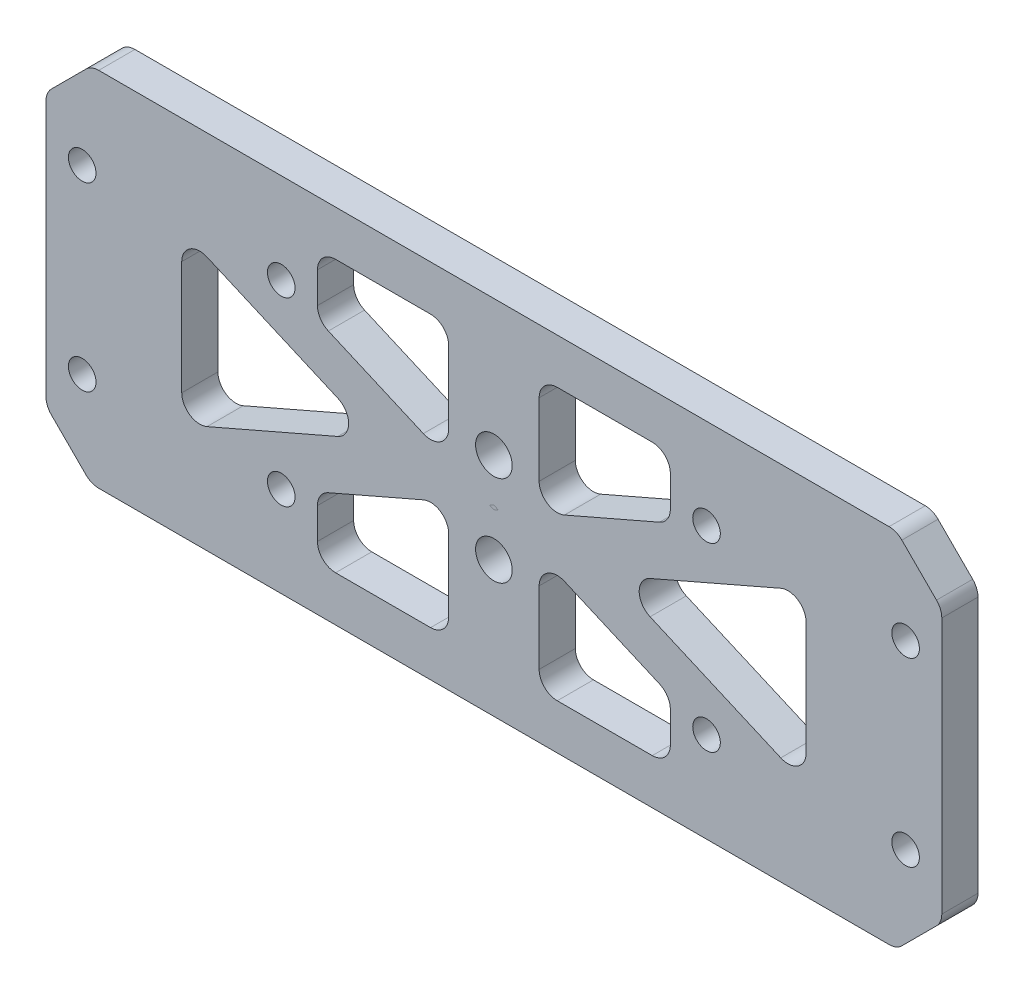
SolidWorks part; units mm, degrees
material "Thornel Mat VMA"
ref_plane "前视基准面" through (0, 0, 0) normal (0, 0, 1) x (1, 0, 0)
ref_plane "上视基准面" through (0, 0, 0) normal (0, 1, 0) x (1, 0, 0)
ref_plane "右视基准面" through (0, 0, 0) normal (1, 0, 0) x (0, 0, -1)
other "Configuration Table"
sketch "草图1" plane through (0, 0, 0) normal (0, 0, 1) x (1, 0, 0)
  line L17 (-49.5, -20) -> (49.5, -20)
  line L18 (-49.5, -20) -> (-49.5, 20)
  line L19 (-49.5, 20) -> (49.5, 20)
  line L20 (49.5, -20) -> (49.5, 20)
  line L21 (-49.5, -20) -> (49.5, 20) construction
  line L22 (-49.5, 20) -> (49.5, -20) construction
  point P0 (0, 0)
  dimension "D1" = 99
  dimension "D2" = 40
extrude "凸台-拉伸1" add sketch "草图1" along normal blind 4
chamfer "倒角1" distance 5 angle 45 4 edges at (49.5, -20, 2) (49.5, 20, 2) (-49.5, -20, 2) (-49.5, 20, 2)
sketch "草图3" plane through (0, 0, 4) normal (0, 0, 1) x (1, 0, 0)
  line L0 (0, 0) -> (-49.5, 0) construction
  line L1 (-49.5, 15) -> (-49.5, -15) construction
  line L2 (0, 0) -> (0, 20) construction
  line L3 (44.5, 20) -> (-44.5, 20) construction
  circle A0 centre (-45.5, 10) radius 1.525
  circle A1 centre (-45.5, -10) radius 1.525
  circle A2 centre (45.5, -10) radius 1.525
  circle A3 centre (45.5, 10) radius 1.525
  dimension "D1" = 3.05
  dimension "D2" = 20
  dimension "D3" = 4
extrude "切除-拉伸1" cut sketch "草图3" against normal blind 10
sketch "草图4" plane through (0, 0, 4) normal (0, 0, 1) x (1, 0, 0)
  line L0 (44.5, 20) -> (-44.5, 20) construction
  line L1 (-34.5, -15) -> (34.5, -15) construction
  line L2 (-34.5, -15) -> (-34.5, 15) construction
  line L3 (-34.5, 15) -> (34.5, 15) construction
  line L4 (34.5, -15) -> (34.5, 15) construction
  line L5 (-34.5, -15) -> (34.5, 15) construction
  line L6 (-34.5, 15) -> (34.5, -15) construction
  line L7 (49.5, -15) -> (49.5, 15) construction
  line L8 (-35, 15) -> (35, 15)
  line L9 (35, 15) -> (0, -0.2174)
  line L10 (0, -0.2174) -> (-35, 15)
  line L11 (-34.5, 9.3305) -> (-34.5, -9.3305)
  line L12 (-34.5, -9.3305) -> (-13.0399, 0)
  line L13 (-13.0399, 0) -> (-34.5, 9.3305)
  line L14 (0, 0) -> (0, -15) construction
  line L15 (0, 0) -> (-13.0399, 0) construction
  line L16 (-35, -15) -> (35, -15)
  line L17 (35, -15) -> (0, 0.2174)
  line L18 (0, 0.2174) -> (-35, -15)
  line L19 (34.5, 9.3305) -> (34.5, -9.3305)
  line L20 (13.0399, 0) -> (34.5, 9.3305)
  line L21 (34.5, -9.3305) -> (13.0399, 0)
  point P0 (0, 0)
  dimension "D1" = 5
  dimension "D2" = 15
  dimension "D3" = 5
  dimension "D4" = 70
extrude "切除-拉伸2" cut sketch "草图4" against normal blind 10 contours L18 L17 L9 L8 L10 | L10 L18 L16 L17 L9 | L12 L13 L11 | L21 L19 L20
sketch "草图5" plane through (0, 0, 4) normal (0, 0, 1) x (1, 0, 0)
  line L0 (35, 15) -> (-35, 15) construction
  line L3 (-5, -15) -> (5, -15)
  line L4 (-5, -15) -> (-5, 15)
  line L6 (-5, 15) -> (5, 15)
  line L7 (5, -15) -> (5, 15)
  line L8 (-5, -15) -> (5, 15) construction
  line L9 (-5, 15) -> (5, -15) construction
  point P0 (0, 0)
  dimension "D1" = 10
extrude "凸台-拉伸2" add sketch "草图5" against normal up to surface (4 mm away) up to face at (0, 0, 0)
fillet "圆角2" radius 2 18 edges at (34.5, -9.3305, 2) (34.5, 9.3305, 2) (13.0399, 0, 2) (-34.5, -9.3305, 2) (-13.0399, 0, 2) (-34.5, 9.3305, 2) (5, 1.9565, 2) (35, 15, 2) (5, 15, 2) (-35, -15, 2) (-5, -15, 2) (-5, -1.9565, 2) (5, -15, 2) (35, -15, 2) (5, -1.9565, 2) (-5, 15, 2) (-35, 15, 2) (-5, 1.9565, 2)
fillet "圆角3" radius 2 8 edges at (49.5, 15, 2) (44.5, 20, 2) (-49.5, 15, 2) (-49.5, -15, 2) (-44.5, -20, 2) (44.5, -20, 2) (49.5, -15, 2) (-44.5, 20, 2)
sketch "草图6" plane through (0, 0, 0) normal (0, 0, -1) x (-1, 0, 0)
  line L0 (-19.5, 8.2609) -> (-19.5, 15)
  line L1 (-7.7975, 3.1728) -> (-26.1815, 11.1659) construction
  line L2 (-19.5, -312.5) -> (-19.5, 87.5) construction
  line L3 (-25.384, 15) -> (-7, 15) construction
  line L4 (-19.5, 15) -> (-35, 15)
  line L5 (-35, 15) -> (-19.5, 8.2609)
  line L6 (0, 0) -> (-16.0559, 0) construction
  line L7 (0, 0) -> (0, 20) construction
  line L8 (-43.6716, 20) -> (43.6716, 20) construction
  line L9 (35, 15) -> (19.5, 8.2609)
  line L10 (19.5, 15) -> (35, 15)
  line L11 (19.5, 8.2609) -> (19.5, 15)
  line L12 (19.5, -8.2609) -> (19.5, -15)
  line L13 (19.5, -15) -> (35, -15)
  line L14 (35, -15) -> (19.5, -8.2609)
  line L15 (-35, -15) -> (-19.5, -8.2609)
  line L16 (-19.5, -15) -> (-35, -15)
  line L17 (-19.5, -8.2609) -> (-19.5, -15)
  arc A0 (-17.2585, -1.8341) -> (-17.2585, 1.8341) centre (-18.0559, 0) ccw construction
extrude "凸台-拉伸3" add sketch "草图6" against normal up to surface (4 mm away) up to face at (0, 0, 4)
fillet "圆角4" radius 2 8 edges at (19.5, 8.2609, 2) (-19.5, 8.2609, 2) (-19.5, 15, 2) (-19.5, -8.2609, 2) (-19.5, -15, 2) (19.5, -15, 2) (19.5, -8.2609, 2) (19.5, 15, 2)
sketch "草图7" plane through (0, 0, 0) normal (0, 0, -1) x (-1, 0, 0)
  line L1 (-45.5, 10) -> (-23.5, 10) construction
  line L3 (-19.5, 9.5722) -> (-19.5, 13) construction
  line L4 (0, 0) -> (0, 20) construction
  line L7 (-43.6716, 20) -> (43.6716, 20) construction
  circle A4 centre (-23.5, 10) radius 1.525
  circle A5 centre (-23.5, -10) radius 1.525
  circle A8 centre (23.5, -10) radius 1.525
  circle A9 centre (23.5, 10) radius 1.525
  dimension "D1" = 20
  dimension "D2" = 3.05
  dimension "D3" = 4
extrude "切除-拉伸3" cut sketch "草图7" against normal through all
sketch "草图8" plane through (0, 0, 4) normal (0, 0, 1) x (1, 0, 0)
  line L1 (0, 0) -> (16.0559, 0) construction
  circle A0 centre (0, 5) radius 2.025
  circle A1 centre (0, -5) radius 2.025
  arc A2 (17.2585, 1.8341) -> (17.2585, -1.8341) centre (18.0559, 0) ccw construction
  dimension "D1" = 10
  dimension "D2" = 4.05
extrude "切除-拉伸4" cut sketch "草图8" against normal up to surface (4 mm away) up to face at (0, 0, 0)
